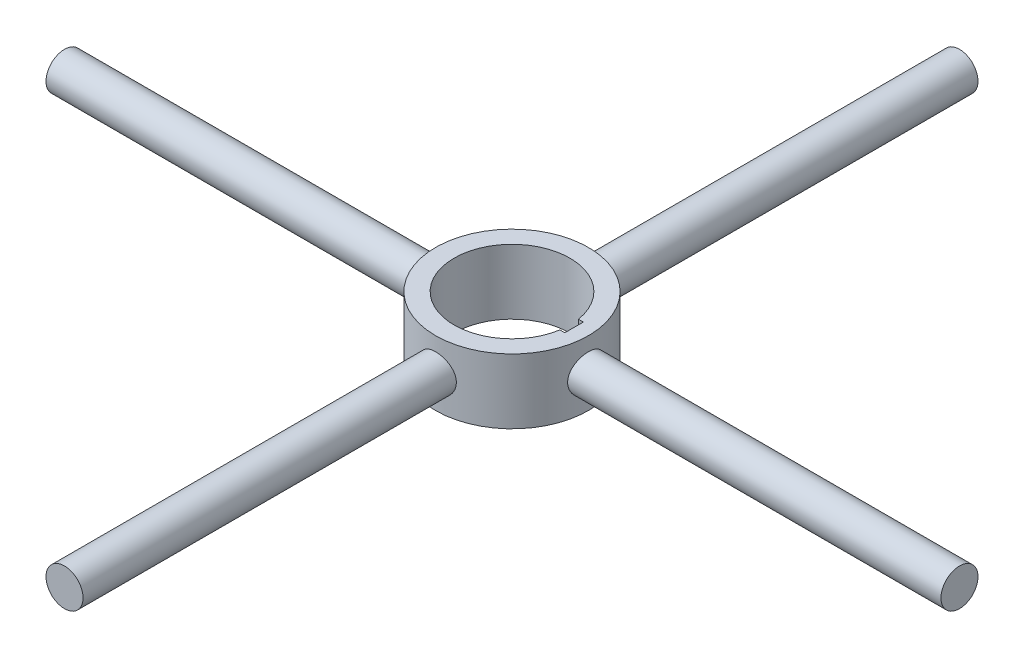
SolidWorks part; units mm, degrees
ref_plane "Ön Düzlem" through (0, 0, 0) normal (0, 0, 1) x (1, 0, 0)
ref_plane "Üst Düzlem" through (0, 0, 0) normal (0, 1, 0) x (1, 0, 0)
ref_plane "Sağ Düzlem" through (0, 0, 0) normal (1, 0, 0) x (0, 0, -1)
sketch "Çizim1" plane through (0, 0, 0) normal (0, 1, 0) x (1, 0, 0)
  circle A0 centre (0, 0) radius 62.5
  circle A1 centre (0, 0) radius 82.5
  dimension "D1" = 125
  dimension "D2" = 165
extrude "Yükseklik-Ekstrüzyon1" add sketch "Çizim1" along normal blind 70
ref_plane "Düzlem1" through (77.9048, 0, 0) normal (1, 0, 0) x (0, 0, -1)
sketch "Çizim2" plane through (77.9048, 0, 0) normal (1, 0, 0) x (0, 0, -1)
  line L0 (82.5, 70) -> (-82.5, 70) construction
  circle A0 centre (0, 35) radius 20
  point P2 (0, 0)
  point P4 (0, 38.8182)
  dimension "D1" = 40
  dimension "D2" = 35
extrude "Yükseklik-Ekstrüzyon2" add sketch "Çizim2" along normal blind 405
pattern_circular "Dairesel Kaplama1" count 4 over 360 about axis through (0, 0, 0) along (0, 1, 0) of "Yükseklik-Ekstrüzyon2"
sketch "Çizim4" plane through (0, 70, 0) normal (0, 1, 0) x (1, 0, 0)
  line L0 (482.9048, 20) -> (80.0391, 20) construction
  line L1 (52, 10) -> (67, 10)
  line L2 (52, 10) -> (52, -10)
  line L3 (52, -10) -> (67, -10)
  line L4 (67, 10) -> (67, -10)
  point P7 (53.0918, -10)
  dimension "D1" = 67
  dimension "D2" = 20
  dimension "D3" = 10
  dimension "D4" = 15
extrude "Kes-Ekstrüzyon1" cut sketch "Çizim4" against normal through all
